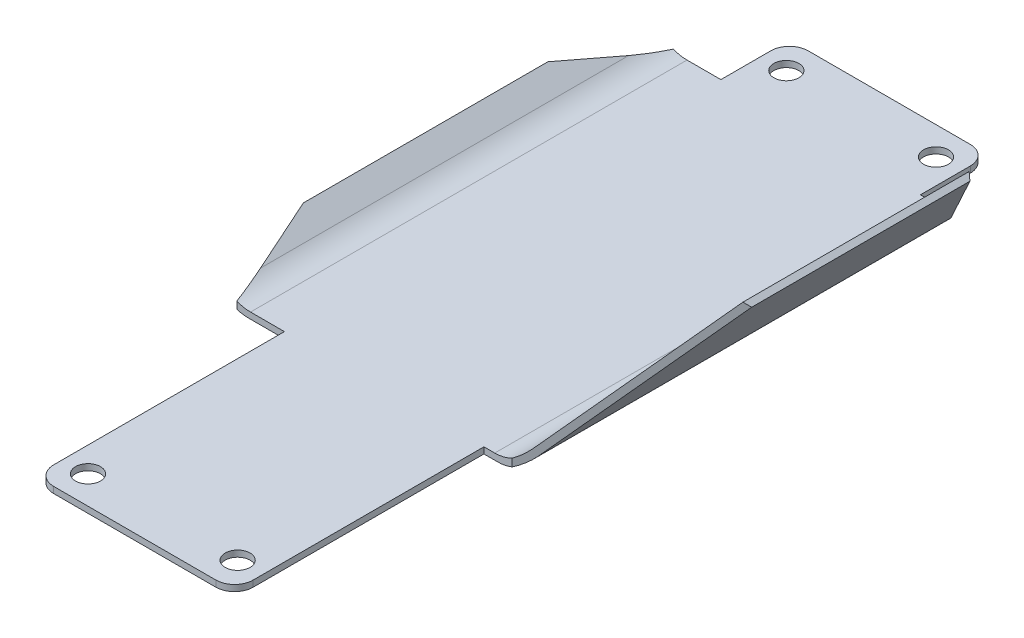
SolidWorks part; units mm, degrees
material "1060 Alloy"
ref_plane "Front Plane" through (0, 0, 0) normal (0, 0, 1) x (1, 0, 0)
ref_plane "Top Plane" through (0, 0, 0) normal (0, 1, 0) x (1, 0, 0)
ref_plane "Right Plane" through (0, 0, 0) normal (1, 0, 0) x (0, 0, -1)
sketch "Sketch1" plane through (0, 0, 0) normal (0, 1, 0) x (1, 0, 0)
  line L0 (0, 60.5) -> (0, -60.5) construction
  line L1 (-13, -60.5) -> (13, -60.5)
  line L2 (-16, -57.5) -> (-16, 57.5)
  line L3 (-13, 60.5) -> (13, 60.5)
  line L4 (16, -57.5) -> (16, 57.5)
  line L5 (-16, -60.5) -> (16, 60.5) construction
  line L6 (-16, 60.5) -> (16, -60.5) construction
  line L7 (-16, 0) -> (16, 0) construction
  circle A0 centre (-12, 56) radius 2
  circle A1 centre (12, 56) radius 2
  circle A2 centre (12, -56) radius 2
  circle A3 centre (-12, -56) radius 2
  arc A4 (-13, -60.5) -> (-16, -57.5) centre (-13, -57.5) cw
  arc A5 (13, -60.5) -> (16, -57.5) centre (13, -57.5) ccw
  arc A6 (-16, 57.5) -> (-13, 60.5) centre (-13, 57.5) cw
  arc A7 (13, 60.5) -> (16, 57.5) centre (13, 57.5) cw
  point P0 (0, 0)
  dimension "D3" = 56
  dimension "D4" = 12
  dimension "D5" = 4
  dimension "D6" = 3
  dimension "D1" = 32
  dimension "D2" = 121
extrude "Boss-Extrude1" add sketch "Sketch1" along normal blind 1
ref_plane "Plane1" through (0, 0, 20.5) normal (0, 0, 1) x (1, 0, 0)
sketch "Sketch2" plane through (0, 0, 20.5) normal (0, 0, 1) x (1, 0, 0)
  line L1 (-23.6333, 1) -> (20.5337, 1)
  line L3 (-24, 0) -> (21, 0)
  line L5 (13, 0) -> (16, 0) construction
  line L6 (16, 1) -> (13, 1) construction
  line L9 (21, 0) -> (41.4381, 24.3572)
  line L10 (20.5337, 1) -> (40.6721, 25)
  line L11 (40.6721, 25) -> (41.4381, 24.3572)
  line L12 (20.234, 0.6428) -> (40.6721, 25) construction
  line L13 (-24, 0) -> (-29, 4.2371)
  line L14 (-23.6333, 1) -> (-28.3535, 5)
  line L15 (-28.3535, 5) -> (-29, 4.2371)
  line L16 (-23.3535, 0.7629) -> (-28.3535, 5) construction
  line L18 (-16, 1) -> (-16, 0) construction
  dimension "D1" = 25
  dimension "D2" = 5
  dimension "D4" = 45
  dimension "D5" = 1
  dimension "D6" = 1
  dimension "D7" = 5
  dimension "D3" = 130
  dimension "D8" = 8
extrude "Boss-Extrude2" add sketch "Sketch2" against normal blind 70
sketch "Sketch3" plane through (0, 0, 0) normal (0, -1, 0) x (1, 0, 0)
  line L0 (-23.6333, 20.5) -> (-29, 3)
  line L1 (-28.3535, -14.5) -> (40.6721, -14.5) construction
  line L2 (-23.6333, -49.5) -> (-29, -32)
  line L3 (20.5337, 20.5) -> (41.4381, 3)
  line L4 (20.5337, -49.5) -> (41.4381, -32)
  line L8 (40.6721, 20.5) -> (20.5337, 20.5)
  line L9 (40.6721, -49.5) -> (40.6721, 20.5)
  line L10 (20.5337, -49.5) -> (40.6721, -49.5)
  line L11 (20.5337, 20.5) -> (20.5337, -49.5)
  line L12 (40.6721, 20.5) -> (20.5337, 20.5)
  line L13 (40.6721, -49.5) -> (40.6721, 20.5)
  line L14 (20.5337, -49.5) -> (40.6721, -49.5)
  line L15 (20.5337, 20.5) -> (20.5337, -49.5)
  line L16 (41.4381, 20.5) -> (21, 20.5)
  line L17 (21, 20.5) -> (21, -49.5)
  line L18 (21, -49.5) -> (41.4381, -49.5)
  line L19 (41.4381, -49.5) -> (41.4381, 20.5)
  line L20 (-23.6333, 20.5) -> (-28.3535, 20.5)
  line L21 (-23.6333, -49.5) -> (-23.6333, 20.5)
  line L22 (-28.3535, -49.5) -> (-23.6333, -49.5)
  line L23 (-28.3535, 20.5) -> (-28.3535, -49.5)
  line L24 (-23.6333, 20.5) -> (-28.3535, 20.5)
  line L25 (-23.6333, -49.5) -> (-23.6333, 20.5)
  line L26 (-28.3535, -49.5) -> (-23.6333, -49.5)
  line L27 (-28.3535, 20.5) -> (-28.3535, -49.5)
  line L28 (41.4381, 20.5) -> (21, 20.5)
  line L29 (21, 20.5) -> (21, -49.5)
  line L30 (21, -49.5) -> (41.4381, -49.5)
  line L31 (41.4381, -49.5) -> (41.4381, 20.5)
  line L44 (-24, 20.5) -> (-29, 20.5)
  line L45 (-29, 20.5) -> (-29, -49.5)
  line L46 (-29, -49.5) -> (-24, -49.5)
  line L47 (-24, -49.5) -> (-24, 20.5)
  line L48 (-16, -49.5) -> (-16, -57.5)
  line L49 (-23.6333, -49.5) -> (-16, -49.5)
  line L50 (-23.6333, 20.5) -> (-23.6333, -49.5)
  line L51 (-16, 20.5) -> (-23.6333, 20.5)
  line L52 (-16, 57.5) -> (-16, 20.5)
  line L53 (13, 60.5) -> (-13, 60.5)
  line L54 (16, 20.5) -> (16, 57.5)
  line L55 (20.5337, 20.5) -> (16, 20.5)
  line L56 (20.5337, -49.5) -> (20.5337, 20.5)
  line L57 (16, -49.5) -> (20.5337, -49.5)
  line L58 (16, -57.5) -> (16, -49.5)
  line L59 (-13, -60.5) -> (13, -60.5)
  line L60 (-16, -49.5) -> (-16, -57.5)
  line L61 (-23.6333, -49.5) -> (-16, -49.5)
  line L62 (-23.6333, 20.5) -> (-23.6333, -49.5)
  line L63 (-16, 20.5) -> (-23.6333, 20.5)
  line L64 (-16, 57.5) -> (-16, 20.5)
  line L65 (13, 60.5) -> (-13, 60.5)
  line L66 (16, 20.5) -> (16, 57.5)
  line L67 (20.5337, 20.5) -> (16, 20.5)
  line L68 (20.5337, -49.5) -> (20.5337, 20.5)
  line L69 (16, -49.5) -> (20.5337, -49.5)
  line L70 (16, -57.5) -> (16, -49.5)
  line L71 (-13, -60.5) -> (13, -60.5)
  line L72 (-24, 20.5) -> (-29, 20.5)
  line L73 (-29, 20.5) -> (-29, -49.5)
  line L74 (-29, -49.5) -> (-24, -49.5)
  line L75 (-24, -49.5) -> (-24, 20.5)
  arc A8 (-13, 60.5) -> (-16, 57.5) centre (-13, 57.5) ccw
  arc A9 (16, 57.5) -> (13, 60.5) centre (13, 57.5) ccw
  arc A10 (13, -60.5) -> (16, -57.5) centre (13, -57.5) ccw
  arc A11 (-16, -57.5) -> (-13, -60.5) centre (-13, -57.5) ccw
  arc A12 (-13, 60.5) -> (-16, 57.5) centre (-13, 57.5) ccw
  arc A13 (16, 57.5) -> (13, 60.5) centre (13, 57.5) ccw
  arc A14 (13, -60.5) -> (16, -57.5) centre (13, -57.5) ccw
  arc A15 (-16, -57.5) -> (-13, -60.5) centre (-13, -57.5) ccw
  line M37 (16, -49.5) -> (21, -49.5)
  line M38 (21, -49.5) -> (21, 20.5)
  line M39 (21, 20.5) -> (16, 20.5)
  line M45 (-16, 20.5) -> (-24, 20.5)
  line M46 (-24, 20.5) -> (-24, -49.5)
  line M47 (-24, -49.5) -> (-16, -49.5)
  dimension "D6" = 17.5
  dimension "D7" = 17.5
  dimension "D1" = 0
  dimension "D2" = 0
  dimension "D3" = 0
  dimension "D4" = 0
  dimension "D5" = 0
extrude "Cut-Extrude1" cut sketch "Sketch3" against normal blind 70 contours L3 L13 L12 M38 | L3 M39 M38 | L3 L31 L28 L13 | L30 L31 L4 L13 | L14 L13 L4 M38 | L2 M47 M46 | L2 L27 L26 M46 | L73 L74 L27 L2 | L0 M45 M46 | L24 L27 L0 M46 | L72 L73 L0 L27 | L4 M37 M38
fillet "Fillet1" radius 6 2 edges at (-23.6333, 1, -14.5) (20.5337, 1, -14.5)
fillet "Fillet2" radius 6 2 edges at (-24, 0, -14.5) (21, 0, -14.5)
